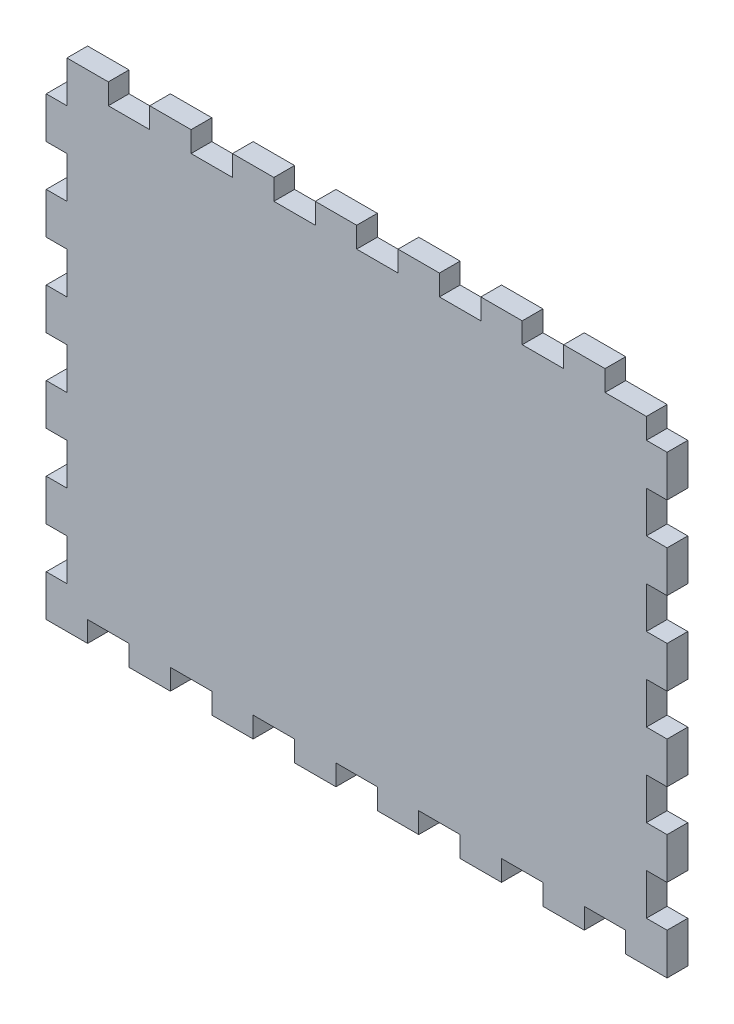
SolidWorks part; units mm, degrees
ref_plane "Front Plane" through (0, 0, 0) normal (0, 0, 1) x (1, 0, 0)
ref_plane "Top Plane" through (0, 0, 0) normal (0, 1, 0) x (1, 0, 0)
ref_plane "Right Plane" through (0, 0, 0) normal (1, 0, 0) x (0, 0, -1)
sketch "Sketch1" plane through (0, 0, 0) normal (0, 0, 1) x (1, 0, 0)
  line L1 (-95.25, 76.2) -> (95.25, 76.2)
  line L2 (-95.25, 76.2) -> (-95.25, -76.2)
  line L3 (-95.25, -76.2) -> (95.25, -76.2)
  line L4 (95.25, 76.2) -> (95.25, -76.2)
  line L5 (-95.25, 76.2) -> (95.25, -76.2) construction
  line L6 (-95.25, -76.2) -> (95.25, 76.2) construction
  point P0 (0, 0)
  dimension "D1" = 152.4
  dimension "D2" = 190.5
extrude "Boss-Extrude1" add sketch "Sketch1" along normal blind 6.35
sketch "Sketch2" plane through (0, 0, 6.35) normal (0, 0, 1) x (1, 0, 0)
  line L0 (95.25, 76.2) -> (-95.25, 76.2) construction
  line L1 (-76.2, 76.2) -> (-63.5, 76.2)
  line L2 (-76.2, 76.2) -> (-76.2, 69.85)
  line L3 (-76.2, 69.85) -> (-63.5, 69.85)
  line L4 (-63.5, 76.2) -> (-63.5, 69.85)
  dimension "D1" = 6.35
  dimension "D2" = 12.7
  dimension "D3" = 19.05
extrude "Cut-Extrude1" cut sketch "Sketch2" against normal through all
pattern_linear "LPattern1" count 7 spacing 25.4 along (1, 0, 0) of "Cut-Extrude1"
sketch "Sketch3" plane through (0, 0, 6.35) normal (0, 0, 1) x (1, 0, 0)
  line L1 (95.25, 76.2) -> (88.9, 76.2)
  line L2 (95.25, 76.2) -> (95.25, 63.5)
  line L3 (95.25, 63.5) -> (88.9, 63.5)
  line L4 (88.9, 76.2) -> (88.9, 63.5)
  dimension "D1" = 6.35
  dimension "D2" = 12.7
extrude "Cut-Extrude2" cut sketch "Sketch3" against normal through all
pattern_linear "LPattern2" count 6 spacing 25.4 along (0, -1, 0) of "Cut-Extrude2"
mirror "Mirror2" about plane through (0, 0, 0) normal (1, 0, 0) of "LPattern2", "Cut-Extrude2"
sketch "Sketch4" plane through (0, 0, 6.35) normal (0, 0, 1) x (1, 0, 0)
  line L0 (-95.25, -76.2) -> (95.25, -76.2) construction
  line L1 (-82.55, -76.2) -> (-69.85, -76.2)
  line L2 (-82.55, -76.2) -> (-82.55, -69.85)
  line L3 (-82.55, -69.85) -> (-69.85, -69.85)
  line L4 (-69.85, -76.2) -> (-69.85, -69.85)
  dimension "D1" = 6.35
  dimension "D2" = 12.7
  dimension "D3" = 12.7
extrude "Cut-Extrude3" cut sketch "Sketch4" against normal through all
pattern_linear "LPattern3" count 7 spacing 25.4 along (1, 0, 0) of "Cut-Extrude3"
